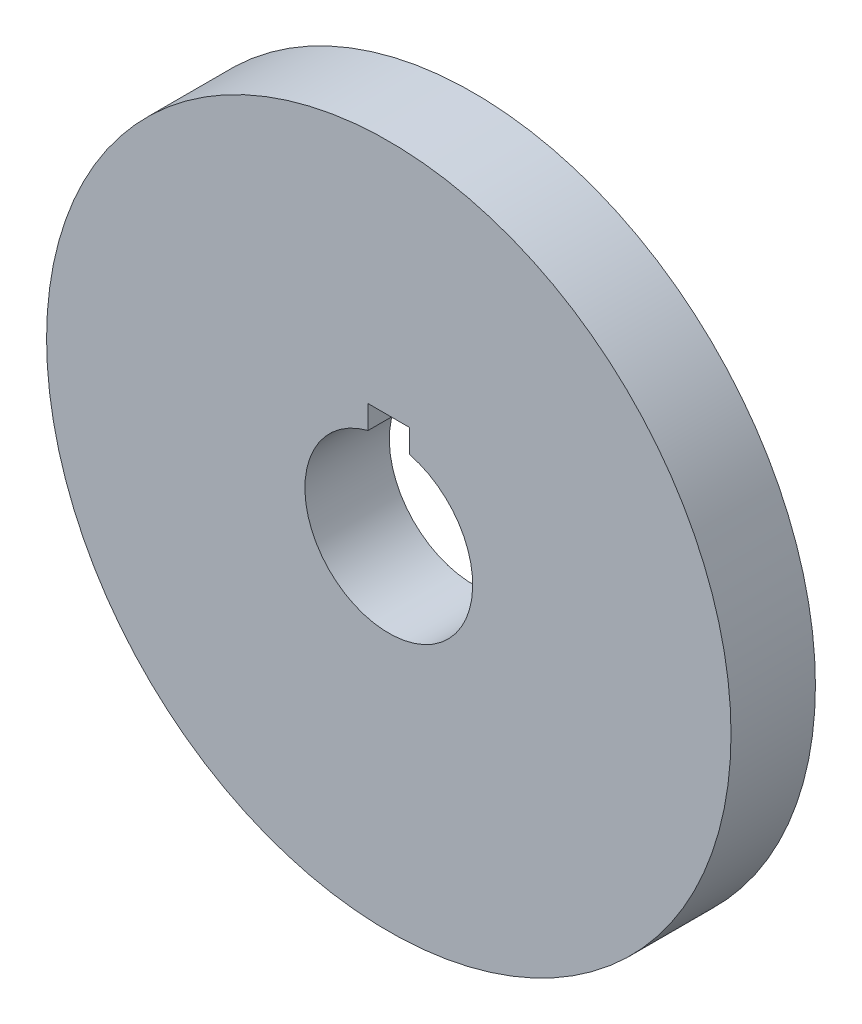
SolidWorks part; units mm, degrees
ref_plane "Front Plane" through (0, 0, 0) normal (0, 0, 1) x (1, 0, 0)
ref_plane "Top Plane" through (0, 0, 0) normal (0, 1, 0) x (1, 0, 0)
ref_plane "Right Plane" through (0, 0, 0) normal (1, 0, 0) x (0, 0, -1)
sketch "Sketch1" plane through (0, 0, 0) normal (0, 0, 1) x (1, 0, 0)
  line L0 (0, -25.75) -> (0, 25.75) construction
  line L1 (-1.5625, 7.875) -> (1.5625, 7.875)
  line L2 (-1.5625, 7.875) -> (-1.5625, 6.1161)
  line L3 (1.5625, 7.875) -> (1.5625, 6.1161)
  circle A0 centre (0, 0) radius 25.75
  arc A1 (-1.5625, 6.1161) -> (1.5625, 6.1161) centre (0, 0) ccw
  point P8 (0, 7.875)
  dimension "D1" = 51.5
  dimension "D2" = 12.625
  dimension "D3" = 3.125
  dimension "D4" = 7.875
extrude "Boss-Extrude1" add sketch "Sketch1" along normal blind 6.35
